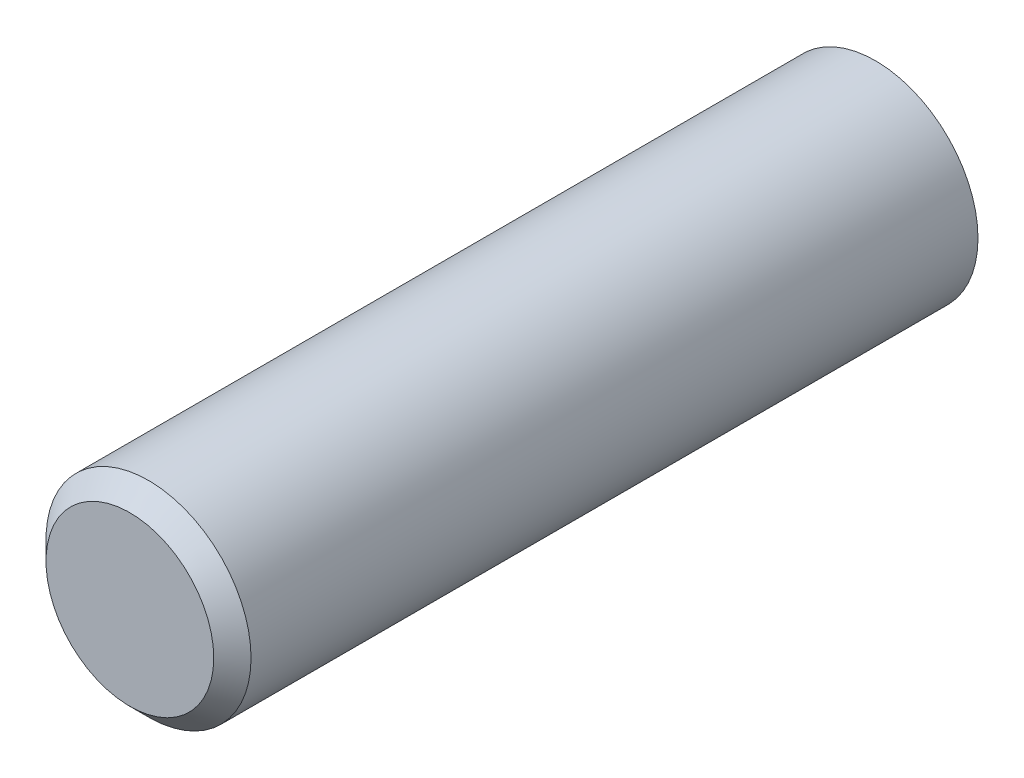
SolidWorks part; units mm, degrees
material "Delrin 2700 NC010, Low Viscosity Acetal Copolymer (SS)"
ref_plane "Front Plane" through (0, 0, 0) normal (0, 0, 1) x (1, 0, 0)
ref_plane "Top Plane" through (0, 0, 0) normal (0, 1, 0) x (1, 0, 0)
ref_plane "Right Plane" through (0, 0, 0) normal (1, 0, 0) x (0, 0, -1)
sketch "Sketch1" plane through (0, 0, 0) normal (0, 0, 1) x (1, 0, 0)
  circle A0 centre (0, 0) radius 5.5
  circle A1 centre (0, 0) radius 4.7
  point P3 (2.9524, 0)
  dimension "D1" = 11
  dimension "D2" = 0.8
extrude "Boss-Extrude1" add sketch "Sketch1" along normal blind 40
sketch "Sketch2" plane through (0, 0, 40) normal (0, 0, 1) x (1, 0, 0)
  circle A0 centre (0, 0) radius 5.5
  circle A1 centre (0, 0) radius 5.5 construction
  point P2 (0, -2.0096)
  point P3 (6.3285, -5.7993)
  point P5 (0, 0)
  point P6 (0, 0)
extrude "Boss-Extrude2" add sketch "Sketch2" against normal blind 2
chamfer "Chamfer1" distance 1 angle 45 1 edges at (5.5, 0, 40)
